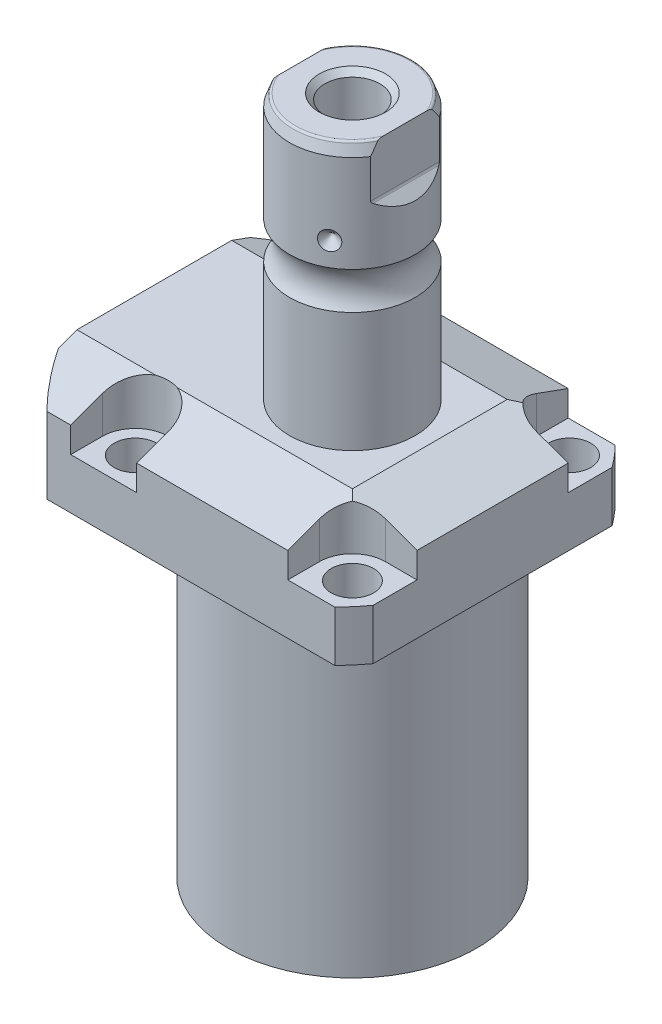
SolidWorks part; units mm, degrees
material "Alloy Steel"
ref_plane "Front Plane" through (0, 0, 0) normal (0, 0, 1) x (1, 0, 0)
ref_plane "Top Plane" through (0, 0, 0) normal (0, 1, 0) x (1, 0, 0)
ref_plane "Right Plane" through (0, 0, 0) normal (1, 0, 0) x (0, 0, -1)
sketch "Sketch1" plane through (0, 0, 0) normal (0, -1, 0) x (0, 0, 1)
  line L0 (-35.433, 50.063) -> (35.433, 50.063)
  line L1 (35.433, 50.063) -> (35.433, -35.433)
  line L2 (35.433, -35.433) -> (-35.433, -35.433)
  line L3 (-35.433, -35.433) -> (-35.433, 50.063)
  line L4 (0, 0) -> (0, -60.6467) construction
  dimension "D1" = 35.433
  dimension "D2" = 85.496
  dimension "D3" = 70.866
extrude "Extrude1" add sketch "Sketch1" against normal blind 104.4448
sketch "Sketch2" plane through (0, 0, 0) normal (0, -1, 0) x (1, 0, 0)
  circle A0 centre (-5.4102, 0) radius 50.8
  dimension "D1" = 101.6
  dimension "D2" = 5.4102
extrude "Cut-Extrude1" cut sketch "Sketch2" against normal through all flip side to cut
sketch "Sketch3" plane through (0, 0, 0) normal (1, 0, 0) x (0, 0, -1)
  line L0 (31.3945, 0) -> (31.3945, 79.4258)
  line L1 (31.3945, 79.4258) -> (76.5937, 79.4258)
  line L2 (76.5937, 79.4258) -> (76.5937, 0)
  line L3 (76.5937, 0) -> (31.3945, 0)
  line L4 (0, -93.345) -> (0, 4.445) construction
  line L5 (24.2233, 0) -> (-24.2233, 0) construction
  dimension "D1" = 62.789
  dimension "D2" = 153.1874
  dimension "D3" = 79.4258
revolve "Cut-Revolve1" cut sketch "Sketch3" angle 360 about L4
fillet "Fillet1" radius 0.381 1 edges at (0, 79.4258, -31.3945)
sketch "Sketch4" plane through (0, 104.4448, 0) normal (0, 1, 0) x (-1, 0, 0)
  line L0 (-35.433, -30.2072) -> (-35.433, 30.2072) construction
  line L1 (41.8127, 35.433) -> (-30.9923, 35.433) construction
  line L2 (-19.1008, -35.433) -> (-19.1008, -27.432)
  line L3 (-35.433, -35.433) -> (-19.1008, -35.433)
  line L4 (-35.433, -19.1008) -> (-35.433, -35.433)
  line L5 (-27.432, -19.1008) -> (-35.433, -19.1008)
  line L6 (35.7632, -35.433) -> (19.1008, -35.433)
  line L7 (19.1008, 35.433) -> (19.1008, 27.432)
  line L8 (35.7632, 35.433) -> (35.7632, 27.432)
  line L9 (35.7632, 35.433) -> (19.1008, 35.433)
  line L10 (-27.432, 19.1008) -> (-35.433, 19.1008)
  line L11 (-35.433, 19.1008) -> (-35.433, 35.433)
  line L12 (-35.433, 35.433) -> (-19.1008, 35.433)
  line L13 (-19.1008, 35.433) -> (-19.1008, 27.432)
  line L14 (-48.9217, 0) -> (49.4551, 0) construction
  line L15 (35.7632, -35.433) -> (35.7632, -27.432)
  line L16 (19.1008, -35.433) -> (19.1008, -27.432)
  arc A0 (19.1008, -27.432) -> (35.7632, -27.432) centre (27.432, -27.432) cw
  arc A1 (-27.432, -19.1008) -> (-19.1008, -27.432) centre (-27.432, -27.432) cw
  arc A2 (-27.432, 19.1008) -> (-19.1008, 27.432) centre (-27.432, 27.432) ccw
  arc A3 (19.1008, 27.432) -> (35.7632, 27.432) centre (27.432, 27.432) ccw
  dimension "D2" = 8.3312
  dimension "D1" = 27.432
  dimension "D3" = 27.432
  dimension "D4" = 54.864
extrude "Cut-Extrude2" cut sketch "Sketch4" against normal blind 12.243
sketch "Sketch5" plane through (0, 0, 0) normal (1, 0, 0) x (0, 0, -1)
  line L0 (-19.558, 104.4448) -> (-35.433, 98.6668)
  line L1 (0, 0) -> (0, 154.1081) construction
  line L2 (-19.558, 104.4448) -> (-35.433, 104.4448)
  line L3 (-35.433, 104.4448) -> (-35.433, 98.6668)
  dimension "D1" = 15.875
  dimension "D2" = 20
extrude "Cut-Extrude9" cut sketch "Sketch5" against normal through all and the other way through all
mirror "Mirror1" about plane through (0, 0, 0) normal (0, 0, 1) of "Cut-Extrude9"
sketch "Sketch9" plane through (0, 0, 0) normal (0, 0, 1) x (1, 0, 0)
  line L0 (19.558, 104.4448) -> (35.433, 98.6668)
  line L1 (35.433, 98.6668) -> (35.433, 104.4448)
  line L2 (35.433, 104.4448) -> (19.558, 104.4448)
  dimension "D1" = 15.875
  dimension "D2" = 20
extrude "Cut-Extrude7" cut sketch "Sketch9" against normal through all and the other way through all
ref_plane "Plane14" through (-35.0774, 0, 0) normal (1, 0, 0) x (0, 0, -1)
sketch "Sketch20" plane through (-35.0774, 88.9, -18.1102) normal (1, 0, 0) x (0, 1, 0)
  line L0 (-88.9, 18.1102) -> (39.8401, 18.1102) construction
  line L1 (-7.2797, 32.639) -> (36.9042, 32.639) construction
  line L2 (-9.4742, 38.3413) -> (-8.0264, 38.3413)
  line L3 (-9.4742, -6.1131) -> (-9.4742, 42.3335) construction
  line L4 (-8.0264, 38.3413) -> (-8.0264, 35.8902)
  line L5 (-8.0264, 35.8902) -> (-7.0104, 35.8902)
  line L6 (-7.0104, 35.8902) -> (-7.0104, 33.8836)
  line L7 (-7.0104, 33.8836) -> (3.9624, 33.8836)
  line L8 (3.9624, 33.8836) -> (3.9624, 32.639)
  line L9 (3.9624, 32.639) -> (-9.4742, 32.639)
  line L10 (-9.4742, 38.3413) -> (-9.4742, 32.639)
  dimension "D1" = 14.5288
  dimension "D2" = 11.4046
  dimension "D3" = 1.4478
  dimension "D4" = 6.5024
  dimension "D5" = 1.016
  dimension "D6" = 2.4892
  dimension "D7" = 10.9728
revolve "Cut-Revolve4" cut sketch "Sketch20" angle 360 about L1
mirror "Mirror10" about plane through (0, 0, 0) normal (0, 0, 1) of "Cut-Revolve4"
sketch "Sketch10" plane through (-35.0774, 88.9, -18.1102) normal (1, 0, 0) x (0, 1, 0)
  line L0 (-1.0325, 3.5814) -> (1.5659, 3.5814) construction
  line L1 (3.9624, 4.826) -> (-7.0104, 4.826) construction
  line L2 (-7.0104, 2.3368) -> (3.9624, 2.3368) construction
  line L4 (-9.4742, -12.097) -> (-9.4742, 48.3174) construction
  circle A0 centre (-9.2075, 8.1026) radius 1.1811
  dimension "D1" = 2.3622
  dimension "D2" = 0.2667
  dimension "D3" = 9.0424
revolve "Revolve4" add sketch "Sketch10" angle 360 about L0
mirror "Mirror12" about plane through (0, 0, 0) normal (0, 0, 1) of bodies 135
sketch "Sketch15" plane through (0, 0, 0) normal (1, 0, 0) x (0, 0, -1)
  line L0 (0, 104.4448) -> (15.875, 104.4448)
  line L1 (15.875, 104.4448) -> (15.875, 134.6877)
  line L2 (15.875, 144.1019) -> (15.875, 168.5798)
  line L3 (14.8118, 171.5008) -> (0, 171.5008)
  line L4 (0, 171.5008) -> (0, 104.4448)
  line L5 (0, 250.2908) -> (0, 28.9095) construction
  line L6 (19.558, 104.4448) -> (-19.558, 104.4448) construction
  line L7 (14.8118, 171.5008) -> (15.875, 168.5798)
  line L9 (24.2233, 79.4258) -> (35.433, 79.4258) construction
  arc A0 (15.875, 144.1019) -> (15.875, 134.6877) centre (22.2504, 139.3948) ccw
  dimension "D2" = 20
  dimension "D4" = 7.9248
  dimension "D6" = 28.6512
  dimension "D1" = 92.075
  dimension "D3" = 31.75
  dimension "D5" = 32.106
  dimension "D7" = 2.921
revolve "Revolve3" add sketch "Sketch15" angle 360 about L5
hole_wizard "Hole1" positions "Sketch18" profile "Sketch17" legacy end condition up to next
sketch "Sketch18" plane through (0, 92.2018, 0) normal (0, 1, 0) x (-1, 0, 0)
  arc A0 (35.7632, -27.432) -> (19.1008, -27.432) centre (27.432, -27.432) ccw construction
  arc A1 (19.1008, 27.432) -> (35.7632, 27.432) centre (27.432, 27.432) ccw construction
  arc A2 (-27.432, 19.1008) -> (-19.1008, 27.432) centre (-27.432, 27.432) ccw construction
  arc A3 (-19.1008, -27.432) -> (-27.432, -19.1008) centre (-27.432, -27.432) ccw construction
  point P0 (-27.432, -27.432)
  point P1 (-27.432, 27.432)
  point P3 (27.432, 27.432)
  point P5 (27.432, -27.432)
sketch "Sketch17" plane through (27.432, 92.2018, -27.432) normal (1, 0, 0) x (0, 0, 1)
  line L0 (0, 0) -> (0, 12.776)
  line L1 (0, 12.776) -> (5.3594, 12.776)
  line L2 (5.3594, 12.776) -> (5.3594, 0)
  line L3 (5.3594, 0) -> (0, 0)
  line L4 (0, 110) -> (0, -10) construction
  dimension "Diameter" = 10.7188
  dimension "Depth" = 12.776
chamfer "Chamfer1" distance 0.635 angle 45 2 edges at (-35.0774, 81.8896, 13.2842) (-35.0774, 81.8896, -13.2842)
ref_plane "Plane15" through (0, 91.9226, 0) normal (0, -1, 0) x (1, 0, 0)
sketch "Sketch21" plane through (0, 91.9226, 0) normal (0, -1, 0) x (1, 0, 0)
  line L0 (-57.5495, -12.9794) -> (-2.9353, -12.9794) construction
  line L1 (-50.063, -1.9304) -> (-49.809, -1.9304)
  line L2 (-49.809, -1.9304) -> (-49.809, -6.7564)
  line L3 (-49.809, -6.7564) -> (-47.2563, -7.4404)
  line L4 (-46.6957, -8.001) -> (-30.759, -8.001)
  line L5 (-30.759, -8.001) -> (-30.759, -12.9794)
  line L6 (-30.759, -12.9794) -> (-50.063, -12.9794)
  line L7 (-50.063, 24.2233) -> (-50.063, -24.2233) construction
  line L8 (-50.063, -12.9794) -> (-50.063, -1.9304)
  line L9 (-47.2563, -7.4404) -> (-46.6957, -8.001)
  dimension "D1" = 12.9794
  dimension "D2" = 0.254
  dimension "D3" = 22.098
  dimension "D4" = 45
  dimension "D5" = 2.5527
  dimension "D6" = 9.9568
  dimension "D7" = 19.05
  dimension "D8" = 15
  dimension "D9" = 12.446
revolve "Cut-Revolve5" cut sketch "Sketch21" angle 360 about L0
mirror "Mirror13" about plane through (0, 0, 0) normal (0, 0, 1) of "Cut-Revolve5"
fillet "Fillet2" radius 0.635 1 edges at (0, 171.5008, 14.8118)
sketch "Sketch26" plane through (0, 0, 0) normal (0, 0, 1) x (1, 0, 0)
  line L0 (-39.772, 150.0628) -> (35.3173, 150.0628) construction
  line L1 (-15.875, 152.4758) -> (-13.462, 150.0628)
  line L2 (-15.875, 168.5798) -> (-15.875, 144.1019) construction
  line L3 (-13.462, 150.0628) -> (-15.875, 150.0628)
  line L4 (-15.875, 150.0628) -> (-15.875, 152.4758)
  arc A0 (-15.875, 134.6877) -> (-15.875, 144.1019) centre (-22.2504, 139.3948) ccw construction
  dimension "D1" = 45
  dimension "D2" = 4.826
  dimension "D3" = 10.668
revolve "Cut-Revolve7" cut sketch "Sketch26" angle 360 about L0
pattern_circular "CirPattern1" count 3 over 360 about axis through (0, 250.2908, 0) along (0, 1, 0) of "Cut-Revolve7"
hole_wizard "Hole2" positions "Sketch28" profile "Sketch27" legacy
sketch "Sketch28" plane through (0, 171.5008, 0) normal (0, 1, 0) x (-1, 0, 0)
  circle A0 centre (0, 0) radius 15.875 construction
  point P0 (0, 0)
sketch "Sketch27" plane through (0, 171.5008, 0) normal (1, 0, 0) x (0, 0, 1)
  line L0 (0, 0) -> (0, 28.8121)
  line L1 (0, 28.8121) -> (6.9469, 24.638)
  line L2 (6.9469, 24.638) -> (6.9469, 0)
  line L4 (6.9469, 0) -> (0, 0)
  line L6 (0, 28.8121) -> (-6.9469, 24.638) construction
  line L7 (0, -4.2442) -> (0, 117.3081) construction
  dimension "Diameter" = 13.8938
  dimension "Depth" = 24.638
  dimension "Drill Angle" = 118
sketch "Sketch29" plane through (0, 0, 0) normal (0, 0, 1) x (1, 0, 0)
  line L0 (0, 0) -> (0, 192.0172) construction
  line L1 (13.284, 171.5008) -> (13.284, 158.8008)
  line L2 (14.3672, 171.5008) -> (-14.3672, 171.5008) construction
  line L3 (13.5072, 158.262) -> (16.332, 155.4372)
  line L5 (16.332, 155.4372) -> (16.332, 171.5008)
  line L6 (16.332, 171.5008) -> (13.284, 171.5008)
  line L7 (-16.332, 171.5008) -> (-13.284, 171.5008)
  line L8 (-16.332, 155.4372) -> (-16.332, 171.5008)
  line L9 (-13.5072, 158.262) -> (-16.332, 155.4372)
  line L10 (-13.284, 171.5008) -> (-13.284, 158.8008)
  arc A0 (13.284, 158.8008) -> (13.5072, 158.262) centre (14.046, 158.8008) ccw
  arc A1 (-13.284, 158.8008) -> (-13.5072, 158.262) centre (-14.046, 158.8008) cw
  dimension "D2" = 0.762
  dimension "D1" = 45
  dimension "D3" = 26.568
  dimension "D4" = 12.7
  dimension "D5" = 3.048
extrude "Cut-Extrude10" cut sketch "Sketch29" against normal through all and the other way through all
chamfer "Chamfer2" distance 1.4351 angle 45 1 edges at (0, 171.5008, 6.9469)
